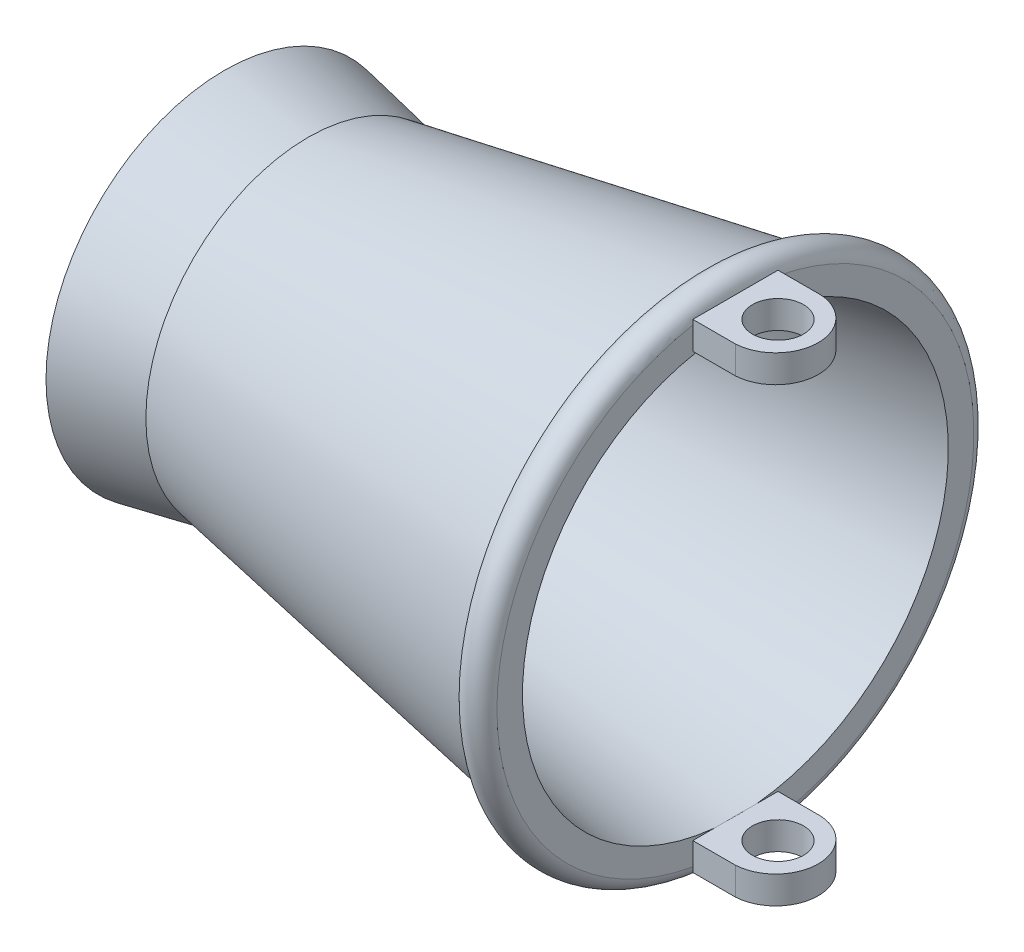
SolidWorks part; units mm, degrees
ref_plane "Front Plane" through (0, 0, 0) normal (0, 0, 1) x (1, 0, 0)
ref_plane "Top Plane" through (0, 0, 0) normal (0, 1, 0) x (1, 0, 0)
ref_plane "Right Plane" through (0, 0, 0) normal (1, 0, 0) x (0, 0, -1)
sketch "Sketch1" plane through (0, 0, 0) normal (0, 1, 0) x (1, 0, 0)
  line L0 (-20.814, 0) -> (35.4204, 0) construction
  line L5 (1.2577, 9.519) -> (24.3808, 13.6484)
  line L6 (26.3497, 14) -> (26.3497, 12.5)
  line L7 (26.3497, 12.5) -> (2.4797, 8.6491)
  line L8 (35.4204, 0) -> (66.0195, 0) construction
  line L9 (0.9797, 8.0625) -> (-3.9316, 9)
  line L10 (1.2577, 9.519) -> (-3.6503, 10.4734)
  line L11 (-3.6503, 10.4734) -> (-3.9316, 9)
  line L12 (0.9797, 8.0625) -> (0.9797, 0)
  line L13 (0.9797, 0) -> (2.4797, 0)
  line L14 (2.4797, 0) -> (2.4797, 8.6491)
  arc A0 (26.3497, 14) -> (24.3808, 13.6484) centre (25.3652, 13.8242) ccw
  dimension "D3" = 1
  dimension "D1" = 5
  dimension "D2" = 5
  dimension "D4" = 1.5
  dimension "D5" = 1.5
  dimension "D6" = 25
  dimension "D7" = 18
  dimension "D8" = 30
  dimension "D9" = 1.5
revolve "Revolve1" add sketch "Sketch1" angle 360 about L0
sketch "Sketch2" plane through (26.3497, 0, 0) normal (1, 0, 0) x (0, 0, -1)
  line L0 (0, 14) -> (0, -14) construction
  line L1 (-14, 0) -> (14, 0) construction
  line L2 (-2.5, 14.0618) -> (2.5, 14.0618)
  line L3 (-2.5, 14.0618) -> (-2.5, 12.4385)
  line L4 (-2.5, 12.4385) -> (2.5, 12.4385)
  line L5 (2.5, 14.0618) -> (2.5, 12.4385)
  line L6 (-2.5, 14.0618) -> (2.5, 12.4385) construction
  line L7 (-2.5, 12.4385) -> (2.5, 14.0618) construction
  line L8 (-2.5, -12.4385) -> (2.5, -12.4385)
  line L9 (2.5, -14.0618) -> (2.5, -12.4385)
  line L10 (-2.5, -14.0618) -> (2.5, -14.0618)
  line L11 (-2.5, -14.0618) -> (-2.5, -12.4385)
  circle A0 centre (0, 0) radius 14 construction
  point P5 (0, 13.2501)
  dimension "D1" = 5
extrude "Boss-Extrude1" add sketch "Sketch2" along normal blind 5
sketch "Sketch3" plane through (0, 14.0618, 0) normal (0, 1, 0) x (1, 0, 0)
  line L0 (28.8497, 2.5) -> (28.8497, -2.5) construction
  line L1 (31.3497, 2.5) -> (26.3497, 2.5) construction
  line L2 (31.3497, -2.5) -> (26.3497, -2.5) construction
  line L3 (28.8497, 2.5) -> (31.3497, 2.5)
  line L4 (31.3497, 2.5) -> (31.3497, -2.5)
  line L5 (31.3497, -2.5) -> (28.8497, -2.5)
  arc A0 (28.8497, 2.5) -> (28.8497, -2.5) centre (28.7135, 0) cw
extrude "Cut-Extrude1" cut sketch "Sketch3" against normal up to surface (26.5003 mm away)
mirror "Mirror1" about plane through (0, 0, 0) normal (0, 1, 0) of "Cut-Extrude1"
sketch "Sketch4" plane through (0, 14.0618, 0) normal (0, 1, 0) x (1, 0, 0)
  line L0 (28.8497, 2.5) -> (28.8497, -2.5) construction
  line L1 (26.3497, 0) -> (31.2172, 0) construction
  line L2 (26.3497, 2.5) -> (26.3497, -2.5) construction
  arc A0 (28.8497, -2.5) -> (28.8497, 2.5) centre (28.7135, 0) ccw construction
  circle A1 centre (28.8497, 0) radius 1.5
  dimension "D1" = 3
extrude "Cut-Extrude2" cut sketch "Sketch4" against normal up to surface (26.5003 mm away)
mirror "Mirror2" about plane through (0, 0, 0) normal (0, 1, 0) of "Cut-Extrude2"
